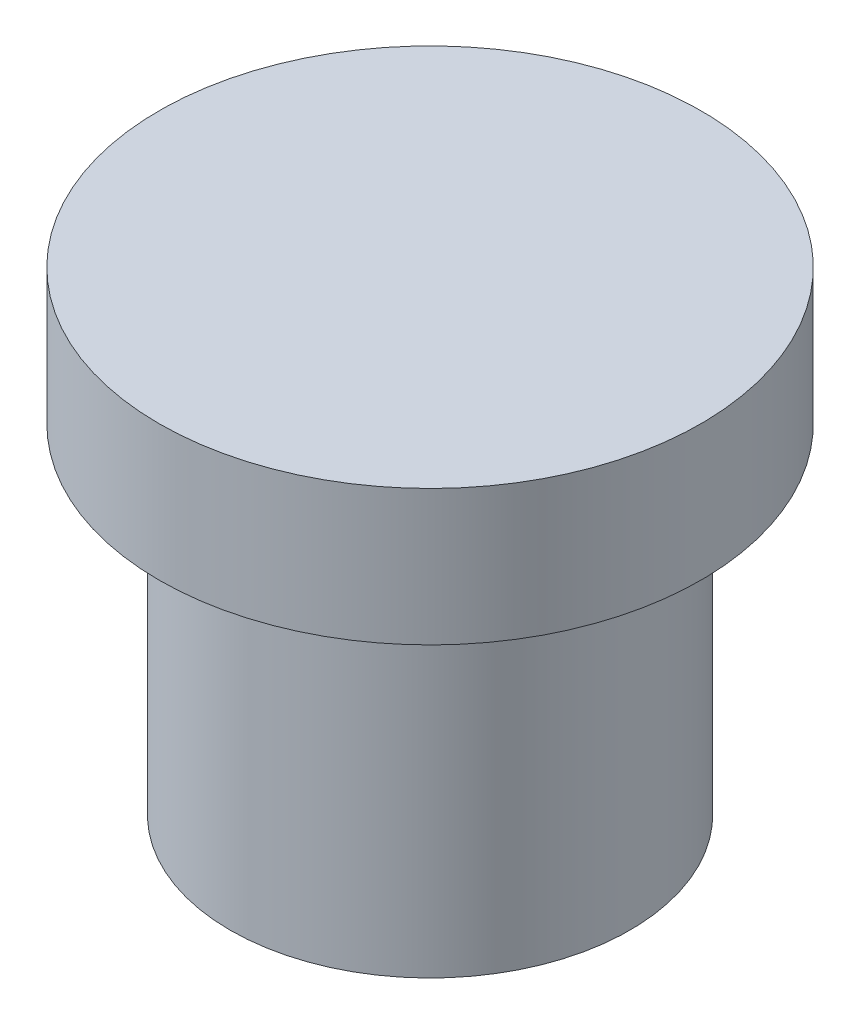
SolidWorks part; units mm, degrees
ref_plane "Спереди" through (0, 0, 0) normal (0, 0, 1) x (1, 0, 0)
ref_plane "Сверху" through (0, 0, 0) normal (0, 1, 0) x (1, 0, 0)
ref_plane "Справа" through (0, 0, 0) normal (1, 0, 0) x (0, 0, -1)
sketch "Sketch1" plane through (0, 0, 0) normal (0, 1, 0) x (1, 0, 0)
  circle A0 centre (0, 0) radius 2.95
  dimension "D1" = 5.9
extrude "Boss-Extrude1" add sketch "Sketch1" along normal blind 5
sketch "Sketch2" plane through (0, 5, 0) normal (0, 1, 0) x (1, 0, 0)
  circle A0 centre (0, 0) radius 4
  dimension "D1" = 8
extrude "Boss-Extrude2" add sketch "Sketch2" along normal blind 2
